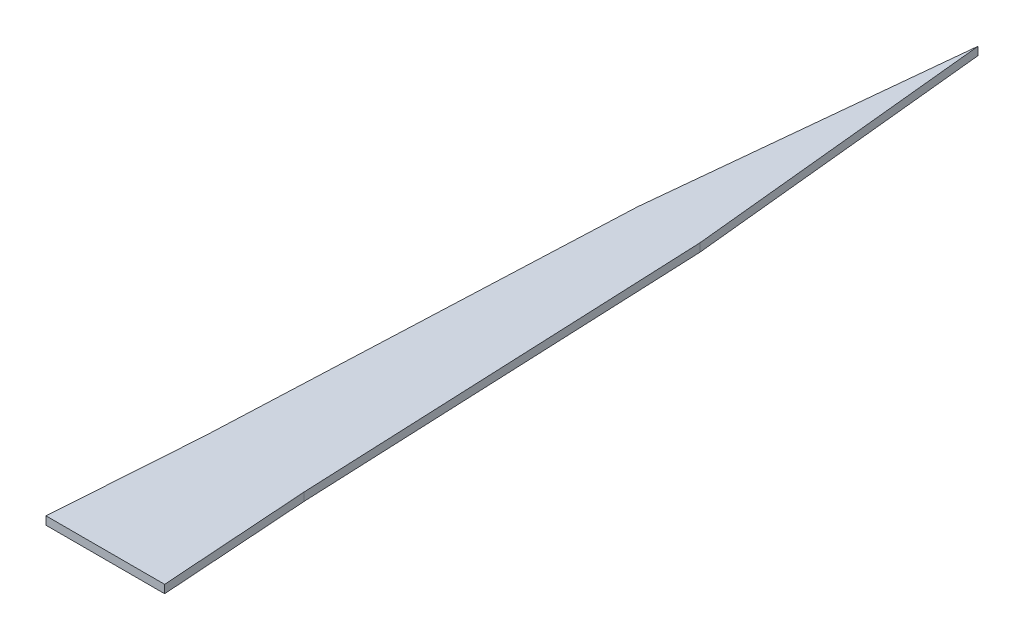
SolidWorks part; units mm, degrees
ref_plane "Plan de face" through (0, 0, 0) normal (0, 0, 1) x (1, 0, 0)
ref_plane "Plan de dessus" through (0, 0, 0) normal (0, 1, 0) x (1, 0, 0)
ref_plane "Plan de droite" through (0, 0, 0) normal (1, 0, 0) x (0, 0, -1)
sketch "Esquisse1" plane through (0, 0, 0) normal (0, 1, 0) x (1, 0, 0)
  line L0 (22.1622, 137.9659) -> (14.5255, 213.6581)
  line L1 (14.5255, 213.6581) -> (6.8887, 137.9659)
  line L2 (6.8887, 137.9659) -> (2.5069, 36.5777)
  line L3 (2.5069, 36.5777) -> (0, 0)
  line L4 (0, 0) -> (29.0509, 0)
  line L5 (29.0509, 0) -> (26.544, 36.5777)
  line L6 (26.544, 36.5777) -> (22.1622, 137.9659)
  point P7 (0, 0)
extrude "Boss.-Extru.1" add sketch "Esquisse1" along normal blind 2
